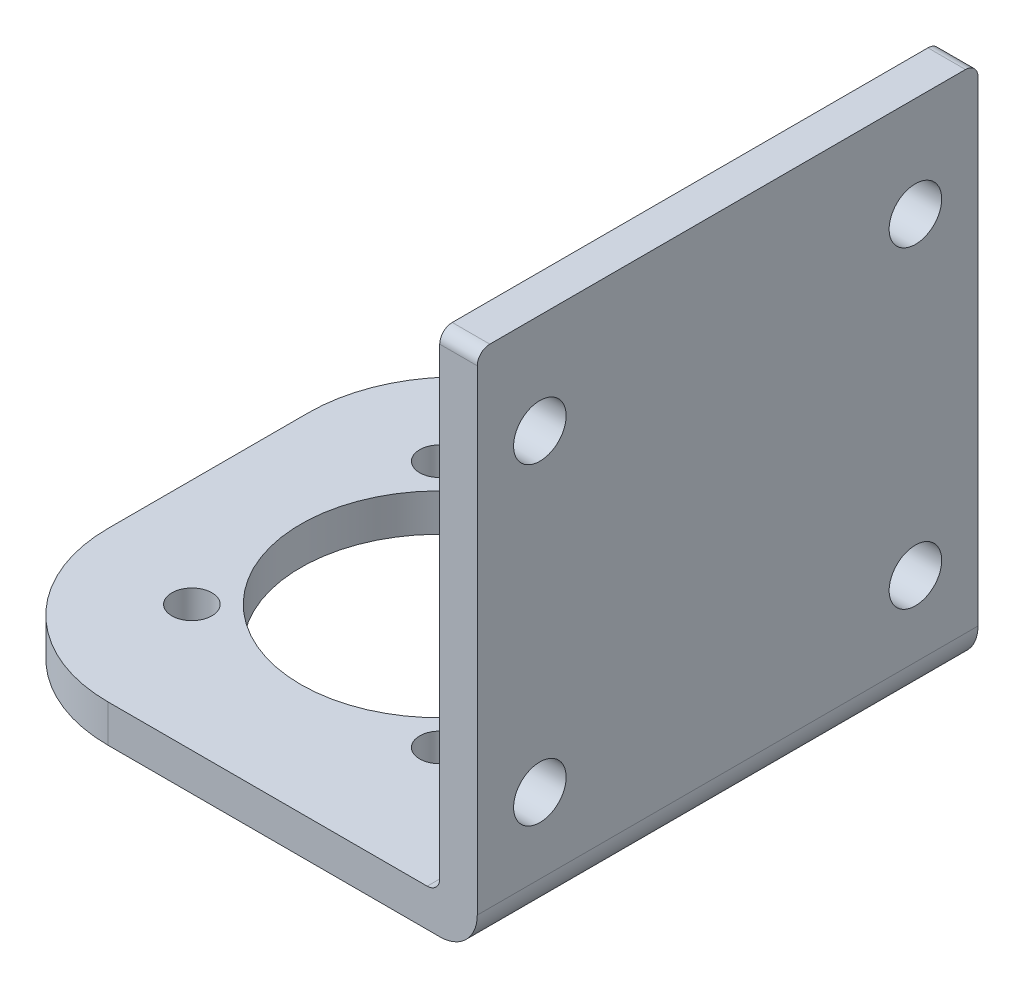
SolidWorks part; units mm, degrees
ref_plane "前视基准面" through (0, 0, 0) normal (0, 0, 1) x (1, 0, 0)
ref_plane "上视基准面" through (0, 0, 0) normal (0, 1, 0) x (1, 0, 0)
ref_plane "右视基准面" through (0, 0, 0) normal (1, 0, 0) x (0, 0, -1)
sketch "草图1" plane through (0, 0, 0) normal (0, 0, 1) x (1, 0, 0)
  line L1 (0, 0) -> (41.5, 0)
  line L2 (0, 0) -> (0, 3)
  line L3 (0, 3) -> (38.5, 3)
  line L4 (41.5, 0) -> (41.5, 3)
  line L5 (41.5, 0) -> (38.5, 0)
  line L6 (41.5, 0) -> (41.5, 42)
  line L7 (41.5, 42) -> (38.5, 42)
  line L8 (38.5, 3) -> (38.5, 42)
  dimension "D1" = 41.5
  dimension "D2" = 3
  dimension "D3" = 39
extrude "凸台-拉伸1" add sketch "草图1" along normal blind 40 contours L8 L3 L2 L1 L4 L6 L7
sketch "草图2" plane through (41.5, 0, 0) normal (1, 0, 0) x (0, 0, -1)
  line L0 (-40, 0) -> (0, 0) construction
  line L3 (-35, 34) -> (-5, 34) construction
  line L4 (-35, 34) -> (-35, 9) construction
  line L5 (-35, 9) -> (-5, 9) construction
  line L6 (-5, 9) -> (-5, 34) construction
  circle A0 centre (-35, 34) radius 2.1
  circle A1 centre (-5, 34) radius 2.1
  circle A2 centre (-35, 9) radius 2.1
  circle A3 centre (-5, 9) radius 2.1
  point P7 (-20, 7.5)
  point P8 (-20, 34)
  dimension "D1" = 9
  dimension "D4" = 4.2
  dimension "D2" = 30
  dimension "D3" = 25
extrude "切除-拉伸1" cut sketch "草图2" against normal blind 3
sketch "草图3" plane through (0, 0, 0) normal (0, -1, 0) x (1, 0, 0)
  line L0 (41.5, 40) -> (41.5, 0) construction
  line L2 (18.5, 20) -> (8.6005, 29.8995) construction
  line L3 (18.5, 20) -> (28.3995, 29.8995) construction
  line L4 (18.5, 20) -> (28.3995, 10.1005) construction
  line L5 (18.5, 20) -> (8.6005, 10.1005) construction
  circle A0 centre (18.5, 20) radius 11.1
  circle A1 centre (18.5, 20) radius 14 construction
  circle A2 centre (8.6005, 29.8995) radius 1.6
  circle A3 centre (28.3995, 29.8995) radius 1.6
  circle A4 centre (28.3995, 10.1005) radius 1.6
  circle A5 centre (8.6005, 10.1005) radius 1.6
  dimension "D2" = 22.2
  dimension "D3" = 28
  dimension "D5" = 90
  dimension "D6" = 90
  dimension "D7" = 90
  dimension "D8" = 3.2
  dimension "D1" = 23
extrude "切除-拉伸2" cut sketch "草图3" against normal blind 3
fillet "圆角1" radius 3 1 edges at (41.5, 0, 20)
fillet "圆角2" radius 12 2 edges at (0, 1.5, 0) (0, 1.5, 40)
fillet "圆角3" radius 1 2 edges at (40, 42, 0) (40, 42, 40)
fillet "圆角4" radius 1 1 edges at (38.5, 3, 20)
sketch "草图4" plane through (41.5, 0, 0) normal (1, 0, 0) x (0, 0, -1)
  line L0 (-20, 42) -> (-20, 0) construction
  line L1 (-39, 42) -> (-1, 42) construction
  line L2 (0, 0) -> (-40, 0) construction
